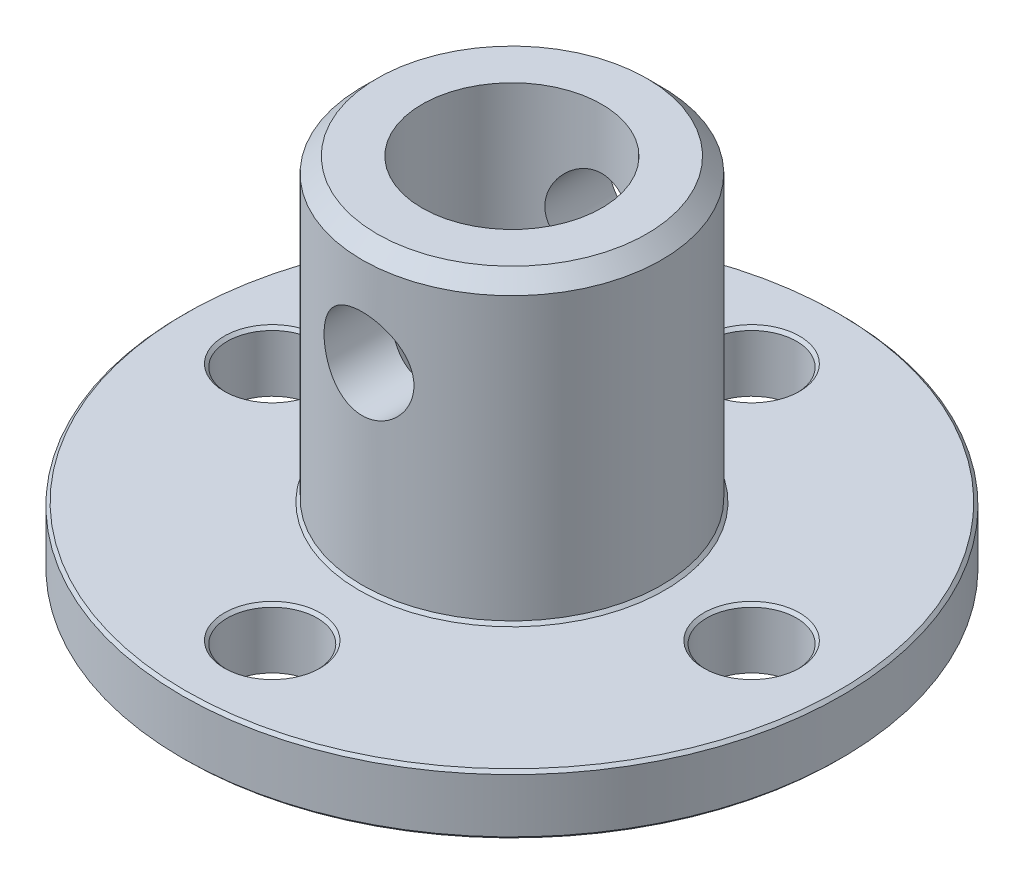
SolidWorks part; units mm, degrees
material "AISI 1020"
ref_plane "Front Plane" through (0, 0, 0) normal (0, 0, 1) x (1, 0, 0)
ref_plane "Top Plane" through (0, 0, 0) normal (0, 1, 0) x (1, 0, 0)
ref_plane "Right Plane" through (0, 0, 0) normal (1, 0, 0) x (0, 0, -1)
sketch "Sketch1" plane through (0, 0, 0) normal (0, 1, 0) x (1, 0, 0)
  line L0 (0, 0) -> (0, 8)
  line L1 (0, 8) -> (0, -8)
  line L2 (0, 0) -> (-8, 0)
  circle A0 centre (0, 0) radius 11
  circle A1 centre (0, 0) radius 3
  circle A2 centre (0, 0) radius 8
  circle A3 centre (0, 8) radius 1.5
  circle A4 centre (8, 0) radius 1.5
  circle A5 centre (0, -8) radius 1.5
  circle A6 centre (-8, 0) radius 1.5
  dimension "D1" = 22
  dimension "D2" = 6
  dimension "D3" = 16
  dimension "D4" = 3
  dimension "D5" = 4
extrude "Boss-Extrude1" add sketch "Sketch1" along normal blind 2 contours A0 A6 A2 A3 A4 A5 | A5 A2 A4 A3 L1 A1 | A6 A2 A5 L1 A1 L2 | A6 L2 A1 L1 A3 A2
sketch "Sketch2" plane through (0, 2, 0) normal (0, 1, 0) x (1, 0, 0)
  circle A0 centre (0, 0) radius 5
  circle A1 centre (0, 0) radius 11
  circle A2 centre (0, 0) radius 11
  circle M5 centre (0, 0) radius 3
  dimension "D2" = 10
  dimension "D1" = 0
extrude "Boss-Extrude2" add sketch "Sketch2" along normal blind 10 contours A0 M5
chamfer "Chamfer1" distance 0.5 angle 45 1 edges at (0, 12, 5)
chamfer "Chamfer2" distance 0.1 angle 45 7 edges at (0, 2, 11) (0, 0, 11) (8, 2, 1.5) (-8, 2, 1.5) (0, 2, 9.5) (0, 2, -6.5) (0, 2, 5)
ref_plane "Plane1" through (0, 0, 5) normal (0, 0, 1) x (1, 0, 0)
sketch "Sketch3" plane through (0, 0, 5) normal (0, 0, 1) x (1, 0, 0)
  line L0 (0, 0) -> (0, 15.3305)
  circle A0 centre (0, 8.5) radius 1.5
  dimension "D1" = 3
  dimension "D2" = 8.5
extrude "Cut-Extrude1" cut sketch "Sketch3" against normal blind 10 contours L0 A0 | L0 A0
